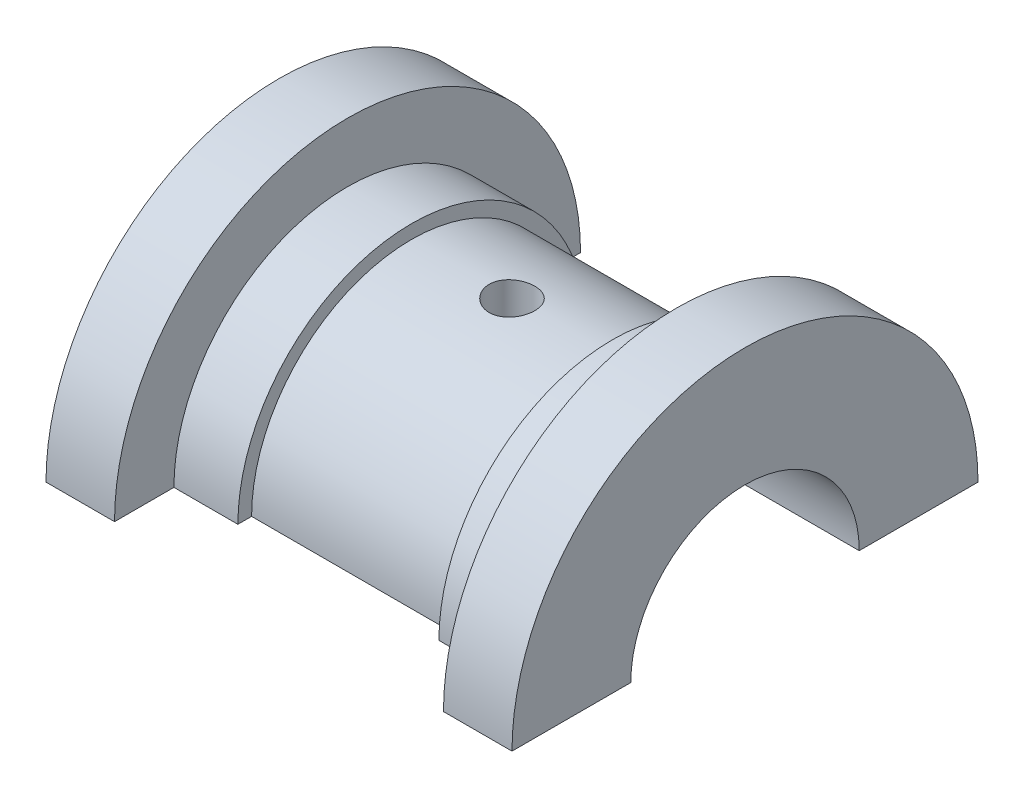
SolidWorks part; units mm, degrees
ref_plane "Front Plane" through (0, 0, 0) normal (0, 0, 1) x (1, 0, 0)
ref_plane "Top Plane" through (0, 0, 0) normal (0, 1, 0) x (1, 0, 0)
ref_plane "Right Plane" through (0, 0, 0) normal (1, 0, 0) x (0, 0, -1)
sketch "Sketch1" plane through (0, 0, 0) normal (0, 0, 1) x (1, 0, 0)
  line L0 (0, 0) -> (0, 59.8387) construction
  line L1 (-25.5, 12.5) -> (25.5, 12.5)
  line L2 (25.5, 12.5) -> (25.5, 25.5)
  line L3 (25.5, 25.5) -> (18, 25.5)
  line L4 (18, 25.5) -> (18, 19)
  line L5 (18, 19) -> (11, 19)
  line L6 (11, 19) -> (11, 17.5)
  line L7 (11, 17.5) -> (-11, 17.5)
  line L8 (-11, 19) -> (-11, 17.5)
  line L9 (-18, 19) -> (-11, 19)
  line L10 (-18, 25.5) -> (-18, 19)
  line L11 (-25.5, 25.5) -> (-18, 25.5)
  line L12 (-25.5, 12.5) -> (-25.5, 25.5)
  line L13 (0, 0) -> (105.6462, 0) construction
  point P12 (0, 17.5)
  point P17 (0, 12.5)
  dimension "D1" = 22
  dimension "D2" = 36
  dimension "D3" = 51
  dimension "D4" = 25
  dimension "D5" = 35
  dimension "D6" = 38
  dimension "D7" = 51
revolve "Revolve1" add sketch "Sketch1" angle 180 mid plane about L13
hole_wizard "Ø5.0mm Dowel Hole1" positions "3DSketch1" profile "Sketch3" hole size "Ø5.0" standard "ANSI Metric"
sketch3d "3DSketch1"
  point P0 (0, 17.5, 0)
  dimension "D1" = 0
  dimension "D2" = 0
sketch "Sketch3" plane through (0, 17.5, 0) normal (1, 0, 0) x (0, 0, 1)
  line L0 (0, 0) -> (0, 7.5022)
  line L1 (0, 7.5022) -> (2.5, 6)
  line L2 (2.5, 6) -> (2.5, 0)
  line L5 (2.5, 0) -> (0, 0)
  line L10 (0, 7.5022) -> (-2.5, 6) construction
  line L11 (0, -6.35) -> (0, 107.95) construction
  dimension "Hole Dia." = 5
  dimension "Hole Depth" = 6
  dimension "Drill Angle" = 118
